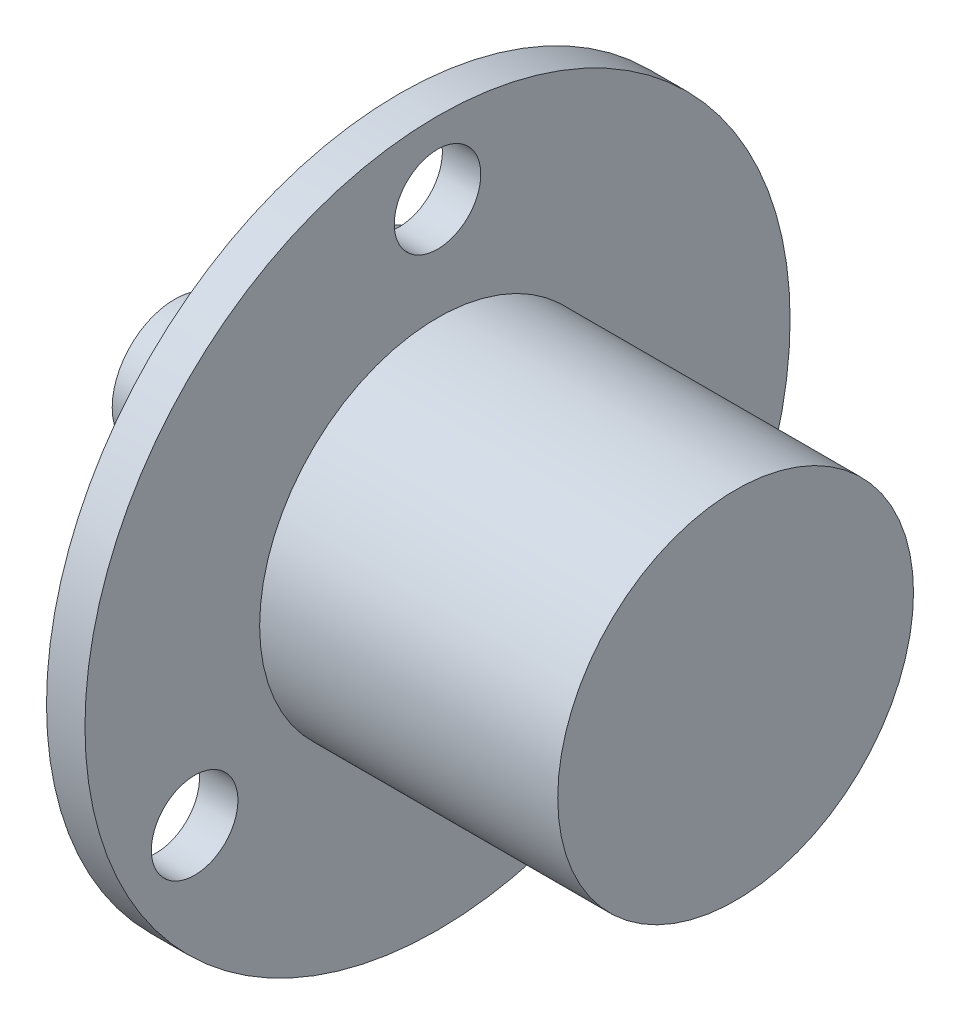
SolidWorks part; units mm, degrees
material "PE High Density"
ref_plane "Front Plane" through (0, 0, 0) normal (0, 0, 1) x (1, 0, 0)
ref_plane "Top Plane" through (0, 0, 0) normal (0, 1, 0) x (1, 0, 0)
ref_plane "Right Plane" through (0, 0, 0) normal (1, 0, 0) x (0, 0, -1)
sketch "Sketch1" plane through (0, 0, 0) normal (0, 0, 1) x (1, 0, 0)
  line L0 (0, 0) -> (35, 0)
  line L1 (35, 0) -> (35, 11.1)
  line L2 (35, 11.1) -> (16.4, 11.1)
  line L3 (16.4, 11.1) -> (16.4, 22)
  line L4 (16.4, 22) -> (14, 22)
  line L5 (14, 22) -> (14, 11.1)
  line L6 (14, 11.1) -> (9, 11.1)
  line L7 (9, 11.1) -> (9, 3.9)
  line L8 (9, 3.9) -> (0, 3.9)
  line L9 (0, 3.9) -> (0, 0)
  dimension "D1" = 3.9
  dimension "D2" = 11.1
  dimension "D3" = 22
  dimension "D4" = 9
  dimension "D5" = 5
  dimension "D6" = 7.4
  dimension "D7" = 26
revolve "Revolve1" add sketch "Sketch1" angle 360 about L0
sketch "Sketch2" plane through (14, 0, 0) normal (-1, 0, 0) x (0, 0, 1)
  line L0 (0, 0) -> (0, 22) construction
  circle A0 centre (0, 0) radius 22 construction
  circle A1 centre (0, 17.5) radius 2.7
  circle A2 centre (15.1554, -8.75) radius 2.7
  circle A3 centre (-15.1554, -8.75) radius 2.7
  point P8 (-16.937, -7.5074)
  point P9 (0, 0)
  point P14 (0, 0)
  dimension "D1" = 5.4
  dimension "D2" = 17.5
  dimension "D3" = 3
extrude "Cut-Extrude1" cut sketch "Sketch2" against normal through all
